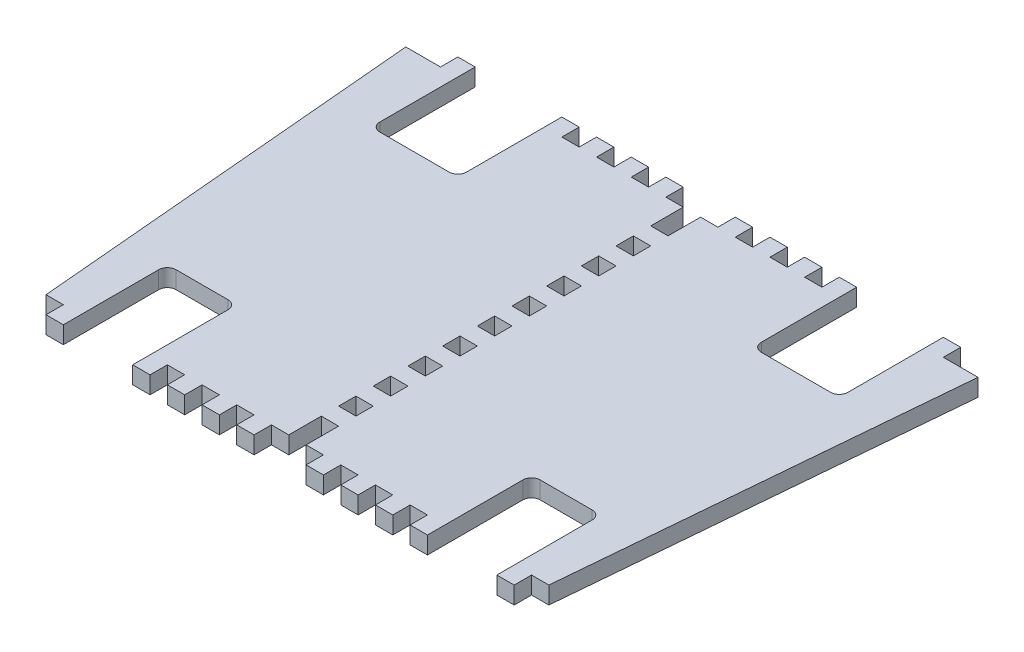
SolidWorks part; units mm, degrees
material "Cedar"
ref_plane "Front Plane" through (0, 0, 0) normal (0, 0, 1) x (1, 0, 0)
ref_plane "Top Plane" through (0, 0, 0) normal (0, 1, 0) x (1, 0, 0)
ref_plane "Right Plane" through (0, 0, 0) normal (1, 0, 0) x (0, 0, -1)
sketch "Sketch1" plane through (0, 0, 0) normal (0, 1, 0) x (1, 0, 0)
  line L0 (-66, 34.0243) -> (-2, 34.0243)
  line L1 (66, 34.0243) -> (58, -56.9757)
  line L2 (58, -56.9757) -> (2, -56.9757)
  line L3 (-58, -56.9757) -> (-66, 34.0243)
  line L4 (0, 34.0243) -> (0, -56.9757) construction
  line L5 (0, -11.4757) -> (15.9946, -11.4757) construction
  line L6 (-2, -1.4757) -> (2, -1.4757)
  line L7 (-2, -9.4757) -> (2, -9.4757)
  line L8 (-2, -9.4757) -> (-2, -13.4757)
  line L9 (-2, -13.4757) -> (2, -13.4757)
  line L10 (2, -9.4757) -> (2, -13.4757)
  line L11 (-2, -1.4757) -> (-2, -5.4757)
  line L12 (-2, -5.4757) -> (2, -5.4757)
  line L13 (2, -1.4757) -> (2, -5.4757)
  line L14 (-2, 6.5243) -> (2, 6.5243)
  line L15 (-2, 6.5243) -> (-2, 2.5243)
  line L16 (-2, 2.5243) -> (2, 2.5243)
  line L17 (2, 6.5243) -> (2, 2.5243)
  line L18 (-2, 14.5243) -> (2, 14.5243)
  line L19 (-2, 14.5243) -> (-2, 10.5243)
  line L20 (-2, 10.5243) -> (2, 10.5243)
  line L21 (2, 14.5243) -> (2, 10.5243)
  line L22 (-2, 22.5243) -> (2, 22.5243)
  line L23 (-2, 22.5243) -> (-2, 18.5243)
  line L24 (-2, 18.5243) -> (2, 18.5243)
  line L25 (2, 22.5243) -> (2, 18.5243)
  line L26 (-2, -17.4757) -> (2, -17.4757)
  line L27 (-2, -17.4757) -> (-2, -21.4757)
  line L28 (-2, -21.4757) -> (2, -21.4757)
  line L29 (2, -17.4757) -> (2, -21.4757)
  line L30 (-2, -25.4757) -> (2, -25.4757)
  line L31 (-2, -25.4757) -> (-2, -29.4757)
  line L32 (-2, -29.4757) -> (2, -29.4757)
  line L33 (2, -25.4757) -> (2, -29.4757)
  line L34 (-2, -33.4757) -> (2, -33.4757)
  line L35 (-2, -33.4757) -> (-2, -37.4757)
  line L36 (-2, -37.4757) -> (2, -37.4757)
  line L37 (2, -33.4757) -> (2, -37.4757)
  line L38 (-2, -41.4757) -> (2, -41.4757)
  line L39 (-2, -41.4757) -> (-2, -45.4757)
  line L40 (-2, -45.4757) -> (2, -45.4757)
  line L41 (2, -41.4757) -> (2, -45.4757)
  line L42 (-2, 34.0243) -> (-2, 26.5243)
  line L43 (-2, 26.5243) -> (2, 26.5243)
  line L44 (2, 26.5243) -> (2, 34.0243)
  line L45 (-2, -56.9757) -> (-2, -49.4757)
  line L46 (-2, -49.4757) -> (2, -49.4757)
  line L47 (2, -49.4757) -> (2, -56.9757)
  line L48 (-2, -56.9757) -> (-58, -56.9757)
  line L49 (2, 34.0243) -> (66, 34.0243)
  line L50 (-2, 34.0243) -> (2, 34.0243) construction
  line L51 (-2, -56.9757) -> (2, -56.9757) construction
  dimension "D1" = 91
  dimension "D2" = 66
  dimension "D3" = 58
  dimension "D4" = 4
  dimension "D5" = 2
  dimension "D6" = 4
  dimension "D8" = 5
  dimension "D7" = 2
  dimension "D10" = 4
  dimension "D11" = 4
  dimension "D12" = 4
  dimension "D13" = 4
  dimension "D14" = 66
  dimension "D15" = 58
  dimension "D9" = 5
extrude "Boss-Extrude1" add sketch "Sketch1" along normal blind 4
sketch "Sketch2" plane through (0, 4, 0) normal (0, 1, 0) x (1, 0, 0)
  line L0 (0, 34.0243) -> (0, 49.0824) construction
  line L1 (-66, 34.0243) -> (-2, 34.0243) construction
  line L2 (-6, 34.0243) -> (-10, 34.0243)
  line L3 (-6, 34.0243) -> (-6, 38.0243)
  line L4 (-6, 38.0243) -> (-10, 38.0243)
  line L5 (-10, 34.0243) -> (-10, 38.0243)
  line L6 (-14, 34.0243) -> (-18, 34.0243)
  line L7 (-14, 34.0243) -> (-14, 38.0243)
  line L8 (-14, 38.0243) -> (-18, 38.0243)
  line L9 (-18, 34.0243) -> (-18, 38.0243)
  line L10 (-22, 34.0243) -> (-26, 34.0243)
  line L11 (-22, 34.0243) -> (-22, 38.0243)
  line L12 (-22, 38.0243) -> (-26, 38.0243)
  line L13 (-26, 34.0243) -> (-26, 38.0243)
  line L14 (-30, 34.0243) -> (-34, 34.0243)
  line L15 (-30, 34.0243) -> (-30, 38.0243)
  line L16 (-30, 38.0243) -> (-34, 38.0243)
  line L17 (-34, 34.0243) -> (-34, 38.0243)
  line L18 (58, 34.0243) -> (58, 38.0243)
  line L19 (54, 38.0243) -> (58, 38.0243)
  line L20 (54, 34.0243) -> (54, 38.0243)
  line L21 (54, 34.0243) -> (58, 34.0243)
  line L22 (34, 34.0243) -> (34, 38.0243)
  line L23 (30, 38.0243) -> (34, 38.0243)
  line L24 (30, 34.0243) -> (30, 38.0243)
  line L25 (30, 34.0243) -> (34, 34.0243)
  line L26 (-54, 34.0243) -> (-58, 34.0243)
  line L27 (-54, 34.0243) -> (-54, 38.0243)
  line L28 (-54, 38.0243) -> (-58, 38.0243)
  line L29 (-58, 34.0243) -> (-58, 38.0243)
  line L30 (-38, 34.0243) -> (-42, 34.0243) [skipped]
  line L31 (-38, 34.0243) -> (-38, 38.0243) [skipped]
  line L32 (-38, 38.0243) -> (-42, 38.0243) [skipped]
  line L33 (-42, 34.0243) -> (-42, 38.0243) [skipped]
  line L34 (-46, 34.0243) -> (-50, 34.0243) [skipped]
  line L35 (-46, 34.0243) -> (-46, 38.0243) [skipped]
  line L36 (-46, 38.0243) -> (-50, 38.0243) [skipped]
  line L37 (-50, 34.0243) -> (-50, 38.0243) [skipped]
  line L38 (26, 34.0243) -> (26, 38.0243)
  line L39 (22, 38.0243) -> (26, 38.0243)
  line L40 (22, 34.0243) -> (22, 38.0243)
  line L41 (22, 34.0243) -> (26, 34.0243)
  line L42 (18, 34.0243) -> (18, 38.0243)
  line L43 (14, 38.0243) -> (18, 38.0243)
  line L44 (14, 34.0243) -> (14, 38.0243)
  line L45 (14, 34.0243) -> (18, 34.0243)
  line L46 (10, 34.0243) -> (10, 38.0243)
  line L47 (6, 38.0243) -> (10, 38.0243)
  line L48 (6, 34.0243) -> (6, 38.0243)
  line L49 (6, 34.0243) -> (10, 34.0243)
  line L50 (58, -56.9757) -> (2, -56.9757) construction
  line L51 (6, -56.9757) -> (10, -56.9757)
  line L52 (6, -56.9757) -> (6, -60.9757)
  line L53 (6, -60.9757) -> (10, -60.9757)
  line L54 (10, -56.9757) -> (10, -60.9757)
  line L55 (0, 34.0243) -> (0, -56.9757) construction
  line L56 (14, -56.9757) -> (18, -56.9757)
  line L57 (14, -56.9757) -> (14, -60.9757)
  line L58 (14, -60.9757) -> (18, -60.9757)
  line L59 (18, -56.9757) -> (18, -60.9757)
  line L60 (22, -56.9757) -> (26, -56.9757)
  line L61 (22, -56.9757) -> (22, -60.9757)
  line L62 (22, -60.9757) -> (26, -60.9757)
  line L63 (26, -56.9757) -> (26, -60.9757)
  line L64 (30, -56.9757) -> (34, -56.9757)
  line L65 (30, -56.9757) -> (30, -60.9757)
  line L66 (30, -60.9757) -> (34, -60.9757)
  line L67 (34, -56.9757) -> (34, -60.9757)
  line L68 (-54, -56.9757) -> (-54, -60.9757)
  line L69 (-50, -60.9757) -> (-54, -60.9757)
  line L70 (-50, -56.9757) -> (-50, -60.9757)
  line L71 (-50, -56.9757) -> (-54, -56.9757)
  line L72 (50, -56.9757) -> (54, -56.9757)
  line L73 (50, -56.9757) -> (50, -60.9757)
  line L74 (50, -60.9757) -> (54, -60.9757)
  line L75 (54, -56.9757) -> (54, -60.9757)
  line L76 (-34, -56.9757) -> (-34, -60.9757)
  line L77 (-30, -60.9757) -> (-34, -60.9757)
  line L78 (-30, -56.9757) -> (-30, -60.9757)
  line L79 (-30, -56.9757) -> (-34, -56.9757)
  line L80 (-26, -56.9757) -> (-26, -60.9757)
  line L81 (-22, -60.9757) -> (-26, -60.9757)
  line L82 (-22, -56.9757) -> (-22, -60.9757)
  line L83 (-22, -56.9757) -> (-26, -56.9757)
  line L84 (-18, -56.9757) -> (-18, -60.9757)
  line L85 (-14, -60.9757) -> (-18, -60.9757)
  line L86 (-14, -56.9757) -> (-14, -60.9757)
  line L87 (-14, -56.9757) -> (-18, -56.9757)
  line L88 (-10, -56.9757) -> (-10, -60.9757)
  line L89 (-6, -60.9757) -> (-10, -60.9757)
  line L90 (-6, -56.9757) -> (-6, -60.9757)
  line L91 (-6, -56.9757) -> (-10, -56.9757)
  dimension "D1" = 6
  dimension "D2" = 4
  dimension "D3" = 4
  dimension "D4" = 6
  dimension "D5" = 4
  dimension "D6" = 4
  dimension "D8" = 4
  dimension "D9" = 2
  dimension "D10" = 16
  dimension "D12" = 16
  dimension "D7" = 4
  dimension "D11" = 2
extrude "Boss-Extrude2" add sketch "Sketch2" against normal up to surface (4 mm away) up to face at (0, 0, 35.4757)
sketch "Sketch3" plane through (0, 4, 0) normal (0, 1, 0) x (1, 0, 0)
  line L0 (-54, 34.0243) -> (-54, 16.0243)
  line L1 (-66, 34.0243) -> (-2, 34.0243) construction
  line L2 (-52, 14.0243) -> (-36, 14.0243)
  line L3 (-34, 16.0243) -> (-34, 34.0243)
  line L6 (-54, 34.0243) -> (-34, 34.0243)
  line L7 (0, 34.0243) -> (0, 50.7514) construction
  line L8 (54, 34.0243) -> (34, 34.0243)
  line L9 (34, 16.0243) -> (34, 34.0243)
  line L10 (52, 14.0243) -> (36, 14.0243)
  line L11 (54, 34.0243) -> (54, 16.0243)
  line L12 (-2, -56.9757) -> (-58, -56.9757) construction
  line L13 (-34, -56.9757) -> (-50, -56.9757)
  line L14 (-34, -56.9757) -> (-34, -38.9757)
  line L15 (-36, -36.9757) -> (-48, -36.9757)
  line L16 (-50, -56.9757) -> (-50, -38.9757)
  line L17 (58, -56.9757) -> (2, -56.9757) construction
  line L18 (34, -56.9757) -> (50, -56.9757)
  line L19 (34, -56.9757) -> (34, -38.9757)
  line L20 (36, -36.9757) -> (48, -36.9757)
  line L21 (50, -56.9757) -> (50, -38.9757)
  arc A0 (-36, 14.0243) -> (-34, 16.0243) centre (-36, 16.0243) ccw
  arc A1 (-54, 16.0243) -> (-52, 14.0243) centre (-52, 16.0243) ccw
  arc A2 (54, 16.0243) -> (52, 14.0243) centre (52, 16.0243) cw
  arc A3 (36, 14.0243) -> (34, 16.0243) centre (36, 16.0243) cw
  arc A4 (48, -36.9757) -> (50, -38.9757) centre (48, -38.9757) cw
  arc A5 (34, -38.9757) -> (36, -36.9757) centre (36, -38.9757) cw
  arc A6 (-34, -38.9757) -> (-36, -36.9757) centre (-36, -38.9757) ccw
  arc A7 (-48, -36.9757) -> (-50, -38.9757) centre (-48, -38.9757) ccw
  point P41 (50, -36.9757)
  point P48 (-50, -36.9757)
  dimension "D4" = 2
  dimension "D7" = 2
  dimension "D1" = 16
  dimension "D2" = 16
  dimension "D3" = 20
  dimension "D5" = 20
  dimension "D6" = 20
extrude "Cut-Extrude2" cut sketch "Sketch3" against normal blind 4
